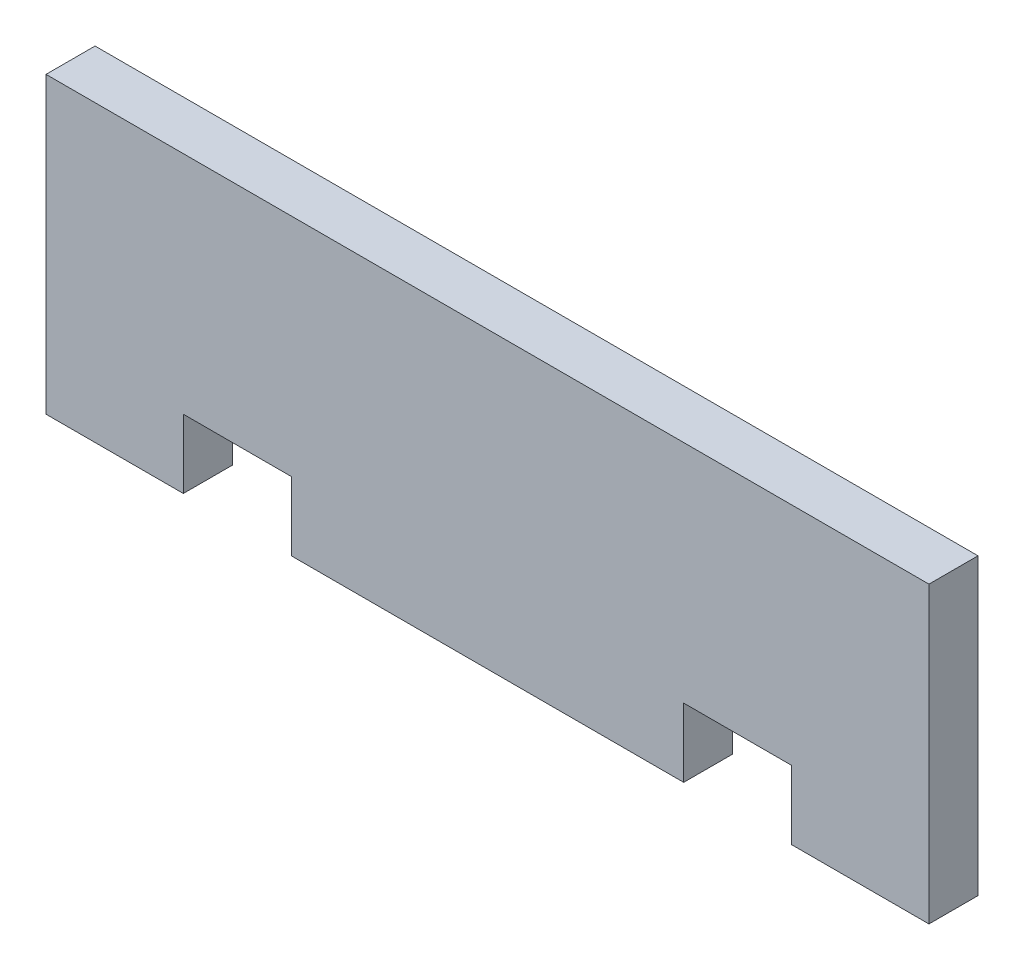
SolidWorks part; units mm, degrees
material "6061 Alloy"
ref_plane "Front Plane" through (0, 0, 0) normal (0, 0, 1) x (1, 0, 0)
ref_plane "Top Plane" through (0, 0, 0) normal (0, 1, 0) x (1, 0, 0)
ref_plane "Right Plane" through (0, 0, 0) normal (1, 0, 0) x (0, 0, -1)
sketch "Sketch1" plane through (0, 0, 0) normal (0, 0, 1) x (1, 0, 0)
  line L0 (-39.37, 8.89) -> (-39.37, 0)
  line L1 (-39.37, 0) -> (-57.15, 0)
  line L2 (-39.37, 8.89) -> (-25.4, 8.89)
  line L3 (-25.4, 8.89) -> (-25.4, 0)
  line L4 (-25.4, 0) -> (25.4, 0)
  line L5 (25.4, 0) -> (25.4, 8.89)
  line L6 (25.4, 8.89) -> (39.37, 8.89)
  line L7 (39.37, 8.89) -> (39.37, 0)
  line L8 (39.37, 0) -> (57.15, 0)
  line L9 (57.15, 0) -> (57.15, 38.1)
  line L10 (57.15, 38.1) -> (-57.15, 38.1)
  line L11 (-57.15, 38.1) -> (-57.15, 0)
  point P1 (0, 0)
  dimension "D1" = 17.78
  dimension "D2" = 17.78
  dimension "D3" = 50.8
  dimension "D4" = 114.3
  dimension "D5" = 38.1
  dimension "D6" = 8.89
extrude "Boss-Extrude1" add sketch "Sketch1" along normal blind 6.35
hole_wizard "9/64 (0.14063) Diameter Hole1" positions "Sketch3" profile "Sketch2" hole size "9/64" standard "Ansi Inch"
sketch "Sketch3" plane through (0, 8.89, 0) normal (0, -1, 0) x (1, 0, 0)
  line L0 (32.766, 6.35) -> (32.766, 0) construction
  line L1 (25.4, 6.35) -> (39.37, 6.35) construction
  line L2 (25.4, 0) -> (39.37, 0) construction
  line L4 (-32.766, 6.35) -> (-32.766, 0) construction
  line L5 (-39.37, 6.35) -> (-25.4, 6.35) construction
  line L6 (-39.37, 0) -> (-25.4, 0) construction
  line L8 (-57.15, 6.35) -> (-57.15, 0) construction
  line L9 (57.15, 6.35) -> (57.15, 0) construction
  point P0 (-32.766, 3.175)
  point P1 (32.766, 3.175)
  point P21 (-32.766, 3.175)
  point P22 (32.766, 3.175)
  dimension "D1" = 24.384
  dimension "D2" = 24.384
sketch "Sketch2" plane through (-32.766, 8.89, 3.175) normal (1, 0, 0) x (0, 0, -1)
  line L0 (0, 0) -> (0, 13.7731)
  line L1 (0, 13.7731) -> (1.786, 12.7)
  line L2 (1.786, 12.7) -> (1.786, 0)
  line L5 (1.786, 0) -> (0, 0)
  line L10 (0, 13.7731) -> (-1.786, 12.7) construction
  line L11 (0, -6.35) -> (0, 107.95) construction
  dimension "Hole Dia." = 3.572
  dimension "Hole Depth" = 12.7
  dimension "Drill Angle" = 118
